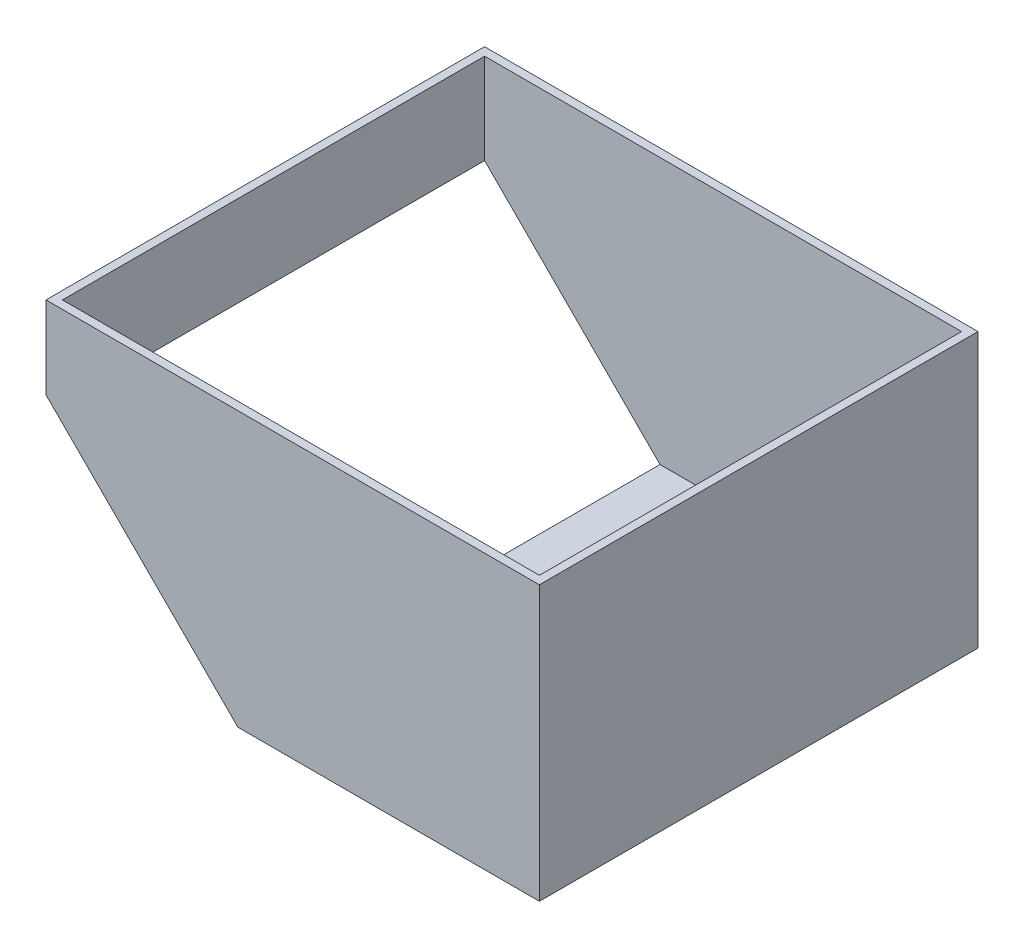
SolidWorks part; units mm, degrees
ref_plane "Front Plane" through (0, 0, 0) normal (0, 0, 1) x (1, 0, 0)
ref_plane "Top Plane" through (0, 0, 0) normal (0, 1, 0) x (1, 0, 0)
ref_plane "Right Plane" through (0, 0, 0) normal (1, 0, 0) x (0, 0, -1)
sketch "Sketch1" plane through (0, 0, 0) normal (0, 1, 0) x (1, 0, 0)
  line L1 (0, 0) -> (180, 0)
  line L2 (0, 0) -> (0, 160)
  line L3 (0, 160) -> (180, 160)
  line L4 (180, 0) -> (180, 160)
  dimension "D1" = 180
  dimension "D2" = 160
extrude "Boss-Extrude1" add sketch "Sketch1" along normal blind 3
sketch "Sketch2" plane through (0, 0, 0) normal (0, 1, 0) x (1, 0, 0)
  line L0 (177, 3) -> (177, 157)
  line L1 (180, 0) -> (0, 0)
  line L2 (180, 0) -> (180, 160)
  line L3 (180, 160) -> (0, 160)
  line L4 (0, 0) -> (0, 160)
  line L5 (177, 157) -> (3, 157)
  line L6 (3, 3) -> (3, 157)
  line L7 (177, 3) -> (3, 3)
  dimension "D1" = 3
extrude "Boss-Extrude2" add sketch "Sketch2" along normal blind 100
sketch "Sketch3" plane through (0, 0, 0) normal (0, 0, 1) x (1, 0, 0)
  line L0 (0, 70) -> (70, 0)
  line L1 (0, 0) -> (180, 0) construction
  line L2 (70, 0) -> (0, 0)
  line L3 (0, 0) -> (0, 70)
  line L4 (0, 100) -> (0, 0) construction
  dimension "D1" = 45
  dimension "D2" = 30
extrude "Cut-Extrude1" cut sketch "Sketch3" against normal through all both and the other way through all
